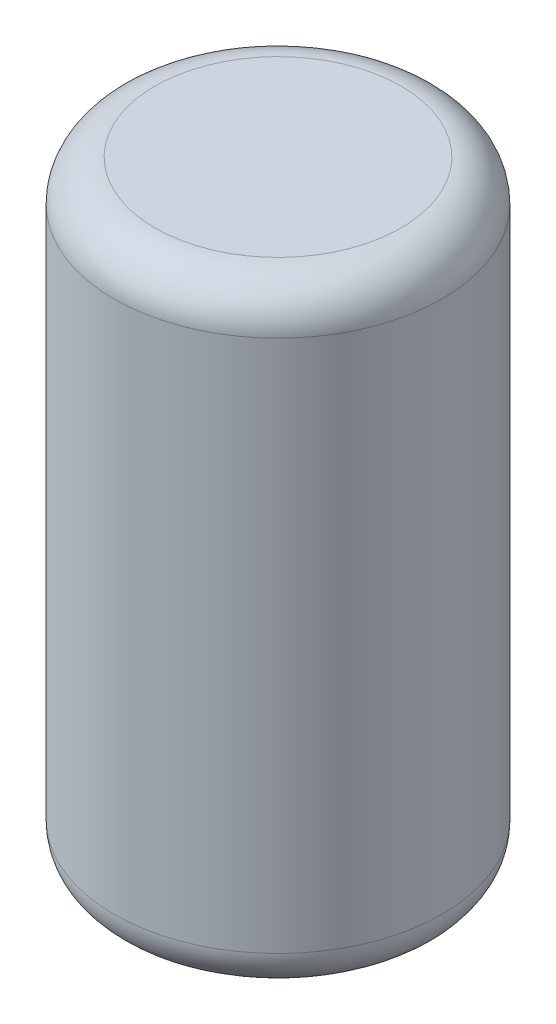
SolidWorks part; units mm, degrees
ref_plane "Front Plane" through (0, 0, 0) normal (0, 0, 1) x (1, 0, 0)
ref_plane "Top Plane" through (0, 0, 0) normal (0, 1, 0) x (1, 0, 0)
ref_plane "Right Plane" through (0, 0, 0) normal (1, 0, 0) x (0, 0, -1)
sketch "Sketch1" plane through (0, 0, 0) normal (0, 1, 0) x (1, 0, 0)
  circle A0 centre (0, 0) radius 4
  dimension "D1" = 8
extrude "Boss-Extrude1" add sketch "Sketch1" along normal blind 15
fillet "Fillet1" radius 1 2 edges at (0, 0, 4) (0, 15, 4)
